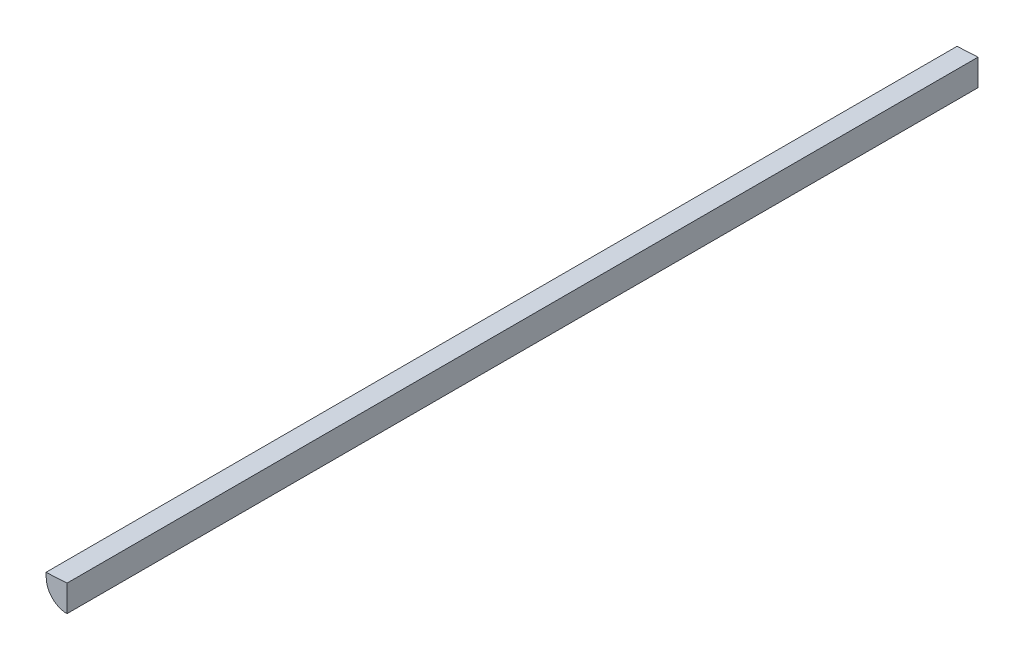
SolidWorks part; units mm, degrees
ref_plane "Front Plane" through (0, 0, 0) normal (0, 0, 1) x (1, 0, 0)
ref_plane "Top Plane" through (0, 0, 0) normal (0, 1, 0) x (1, 0, 0)
ref_plane "Right Plane" through (0, 0, 0) normal (1, 0, 0) x (0, 0, -1)
sketch "Sketch2" plane through (0, 0, 0) normal (0, 0, 1) x (1, 0, 0)
  line L0 (-12.4829, -0.6542) -> (0, -0.6542) construction
  line L2 (-12.4829, -0.6542) -> (0, 0) construction
  line L3 (0, 0) -> (0, -12.5)
  line L4 (0, -12.5) -> (18.0079, -12.5) construction
  line L5 (-13.5227, 19.1875) -> (-12.4829, -0.6542) construction
  line L6 (-12.4829, -0.6542) -> (-12.665, 2.821)
  line L7 (-12.665, 2.821) -> (0, 3.4848)
  line L8 (0, 3.4848) -> (0, 0)
  arc A0 (-12.4829, -0.6542) -> (0, -12.5) centre (0, 0) ccw
  dimension "D1" = 12.5
  dimension "D2" = 93
  dimension "D3" = 3.48
  dimension "D4" = 3
extrude "Boss-Extrude1" add sketch "Sketch2" along normal blind 550
